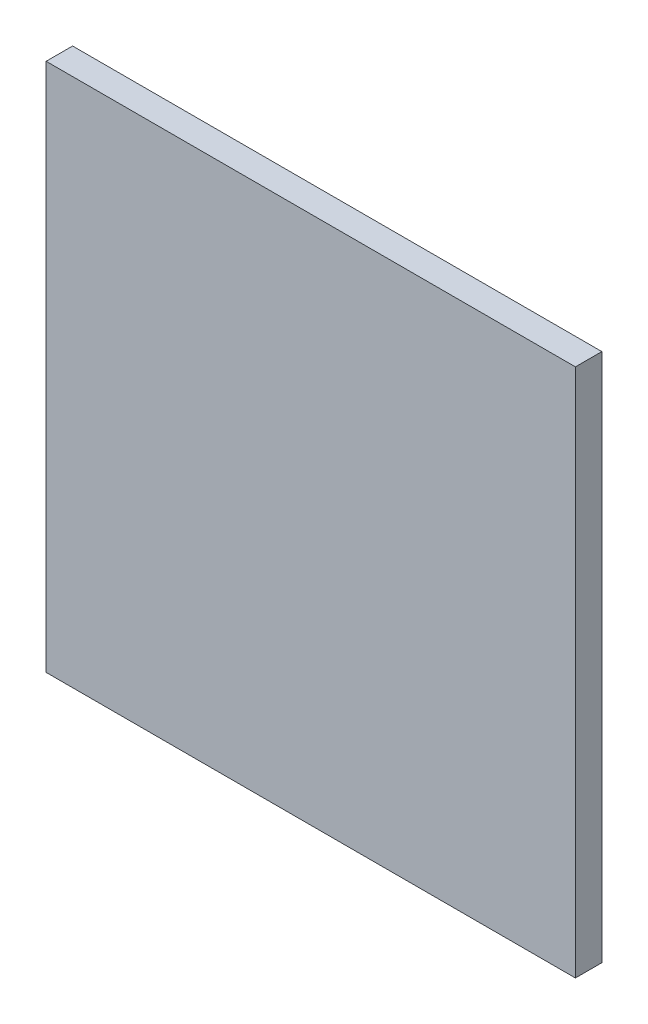
SolidWorks part; units mm, degrees
ref_plane "Piano frontale" through (0, 0, 0) normal (0, 0, 1) x (1, 0, 0)
ref_plane "Piano superiore" through (0, 0, 0) normal (0, 1, 0) x (1, 0, 0)
ref_plane "Piano destro" through (0, 0, 0) normal (1, 0, 0) x (0, 0, -1)
sketch "Schizzo1" plane through (0, 0, 0) normal (0, 0, 1) x (1, 0, 0)
  line L1 (10, 10) -> (-10, 10)
  line L2 (10, 10) -> (10, -10)
  line L3 (10, -10) -> (-10, -10)
  line L4 (-10, 10) -> (-10, -10)
  dimension "D1" = 20
  dimension "D2" = 20
  dimension "D3" = 10
  dimension "D4" = 10
extrude "Estrusione-Estrusione1" add sketch "Schizzo1" along normal blind 1
